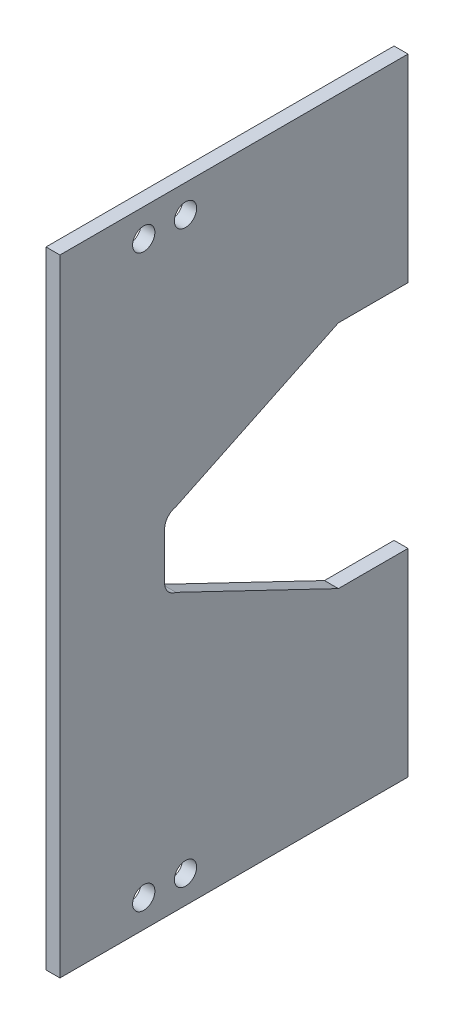
SolidWorks part; units mm, degrees
material "ABS"
ref_plane "前视基准面" through (0, 0, 0) normal (0, 0, 1) x (1, 0, 0)
ref_plane "上视基准面" through (0, 0, 0) normal (0, 1, 0) x (1, 0, 0)
ref_plane "右视基准面" through (0, 0, 0) normal (1, 0, 0) x (0, 0, -1)
ref_plane "基准面4" through (-0.7938, 0, 0) normal (-1, 0, 0) x (0, -1, 0)
sketch "草图1" plane through (-0.7938, 0, 0) normal (-1, 0, 0) x (0, -1, 0)
  line L1 (38.795, 5) -> (12.795, 5)
  line L2 (10.795, 3) -> (10.795, -13)
  line L5 (10.795, 3) -> (55.77, 3) construction
  line L6 (55.77, 3) -> (55.77, -5.0783) construction
  line L7 (55.77, 3) -> (55.77, 5) construction
  line L13 (38.795, 5) -> (72.745, 5)
  line L15 (100.745, 3) -> (100.745, -13)
  line L18 (72.745, 5) -> (98.745, 5)
  line L19 (55.77, 5) -> (55.77, -5.0783) construction
  line L20 (55.77, -5.0783) -> (55.77, -0.0391) construction
  line L21 (55.77, -0.0391) -> (65.77, -0.0391) construction
  line L22 (72.112, -14.1547) -> (62.1308, -0.0391) construction
  line L31 (12.795, -15) -> (47.795, -15)
  line L32 (55.77, -0.0391) -> (50.77, -0.0391)
  line L33 (55.77, -0.0391) -> (60.77, -0.0391)
  line L34 (98.745, -15) -> (63.745, -15)
  line L37 (50.77, -0.0391) -> (47.795, -15)
  line L38 (60.77, -0.0391) -> (63.745, -15)
  arc A2 (12.795, 5) -> (10.795, 3) centre (12.795, 3) ccw
  arc A3 (10.795, -13) -> (12.795, -15) centre (12.795, -13) ccw
  arc A12 (98.745, 5) -> (100.745, 3) centre (98.745, 3) cw
  arc A13 (100.745, -13) -> (98.745, -15) centre (98.745, -13) cw
extrude "凸台-拉伸1" add sketch "草图1" against normal blind 2
fillet "圆角1" radius 2 1 edges at (0.2062, -50.77, -0.0391)
fillet "圆角2" radius 2 1 edges at (0.2063, -47.795, -15)
fillet "圆角3" radius 2 1 edges at (0.2062, -60.77, -0.0391)
fillet "圆角4" radius 2 1 edges at (0.2063, -63.745, -15)
sketch "草图2" plane through (-0.7938, 0, 0) normal (-1, 0, 0) x (0, 0, 1)
  line L0 (5, -55.77) -> (15, -55.77) construction
  line L1 (5, -98.745) -> (5, -12.795) construction
  line L2 (15, -55.77) -> (15, -10.795) construction
  line L3 (15, -55.77) -> (15, -100.745) construction
  line L4 (15, -100.745) -> (3, -100.745) construction
  line L5 (3, -100.745) -> (3, -10.795) construction
  line L6 (3, -10.795) -> (15, -10.795) construction
  line L7 (3, -10.795) -> (15, -10.795)
  line L8 (15, -10.795) -> (15, -100.745)
  line L9 (15, -100.745) -> (3, -100.745)
  line L10 (3, -100.745) -> (3, -10.795)
  line L11 (-15, -29.4743) -> (-25, -29.4743) construction
  line L12 (-15, -12.795) -> (-15, -46.1535) construction
  line L13 (-25, -29.4743) -> (-25, -82.0657) construction
  line L14 (-25, -82.0657) -> (-25, -100.745) construction
  line L15 (-25, -100.745) -> (-13, -100.745) construction
  line L16 (-13, -100.745) -> (-13, -10.795) construction
  line L17 (-13, -10.795) -> (-25, -10.795) construction
  line L18 (-25, -10.795) -> (-25, -29.4743) construction
  line L19 (-1.6491, -50.4499) -> (-13.3901, -48.1151) construction
  line L20 (-13.3901, -48.1151) -> (-25, -45.8065) construction
  line L21 (-1.6491, -61.0901) -> (-13.3901, -63.4249) construction
  line L22 (-13.3901, -63.4249) -> (-25, -65.7335) construction
  line L23 (-25, -10.795) -> (-25, -45.8065)
  line L24 (-25, -45.8065) -> (-13.3901, -48.1151)
  line L26 (-13, -10.795) -> (-25, -10.795)
  line L27 (-13, -10.795) -> (-13.3901, -48.1151)
  line L28 (-13.3901, -63.4249) -> (-25, -65.7335)
  line L29 (-25, -65.7335) -> (-25, -100.745)
  line L30 (-25, -100.745) -> (-13, -100.745)
  line L31 (-13, -100.745) -> (-13.3901, -63.4249)
extrude "凸台-拉伸2" add sketch "草图2" against normal blind 2
sketch "草图5" plane through (1.2062, 0, 0) normal (1, 0, 0) x (0, 0, -1)
  line L0 (25, -10.795) -> (25, -45.8065) construction
  line L1 (25, -45.8065) -> (25, -28.3007) construction
  line L2 (25, -28.3007) -> (25, -37.0536) construction
  line L3 (25, -37.0536) -> (25, -45.8065) construction
  line L4 (25, -45.8065) -> (25, -41.43) construction
  line L5 (25, -41.43) -> (1.6491, -50.4499) construction
  line L6 (1.6491, -50.4499) -> (25, -45.8065)
  line L9 (0.0391, -55.77) -> (-15, -55.77) construction
  line L10 (0.0391, -52.4115) -> (0.0391, -59.1285) construction
  line L11 (-15, -100.745) -> (-15, -10.795) construction
  line L15 (25, -41.43) -> (25, -37.0536) construction
  line L16 (25, -37.0536) -> (25, -39.2418) construction
  line L17 (25, -39.2418) -> (1.6491, -50.4499) construction
  line L18 (1.6491, -50.4499) -> (25, -39.2418)
  line L19 (25, -39.2418) -> (25, -45.8065)
  line L20 (25, -72.2982) -> (25, -65.7335)
  line L21 (1.6491, -61.0901) -> (25, -65.7335)
  line L22 (1.6491, -61.0901) -> (25, -72.2982)
extrude "切除-拉伸1" cut sketch "草图5" against normal blind 10
sketch "草图7" plane through (1.2062, 0, 0) normal (1, 0, 0) x (0, 0, -1)
  line L0 (-15, -55.77) -> (0.0391, -55.77) construction
  line L1 (-15, -100.745) -> (-15, -10.795) construction
  line L2 (0.0391, -52.4115) -> (0.0391, -59.1285) construction
  line L3 (0.0391, -10.795) -> (0.0391, -14.795) construction
  line L4 (-15, -10.795) -> (25, -10.795) construction
  line L5 (-15, -10.795) -> (0.0391, -10.795) construction
  line L6 (0.0391, -14.795) -> (3.0391, -14.795) construction
  line L7 (0.0391, -14.795) -> (-2.9609, -14.795) construction
  circle A0 centre (-2.9609, -14.795) radius 1.6
  circle A1 centre (3.0391, -14.795) radius 1.6
  circle A2 centre (3.0391, -96.745) radius 1.6
  circle A3 centre (-2.9609, -96.745) radius 1.6
extrude "切除-拉伸2" cut sketch "草图7" against normal blind 10
sketch "草图8" plane through (-0.7938, 0, 0) normal (-1, 0, 0) x (0, 0, 1)
  line L0 (-25, -100.745) -> (-35, -100.745) construction
  line L1 (-35, -100.745) -> (-35, -72.2982) construction
  line L2 (-35, -72.2982) -> (-25, -72.2982) construction
  line L3 (-25, -10.795) -> (-35, -10.795) construction
  line L4 (-25, -39.2418) -> (-35, -39.2418) construction
  line L5 (-35, -39.2418) -> (-35, -10.795) construction
  line L6 (-35, -10.795) -> (-25, -10.795)
  line L7 (-25, -10.795) -> (-25, -39.2418)
  line L8 (-35, -10.795) -> (-35, -39.2418)
  line L9 (-35, -39.2418) -> (-25, -39.2418)
  line L10 (-35, -72.2982) -> (-25, -72.2982)
  line L11 (-25, -72.2982) -> (-25, -100.745)
  line L12 (-25, -100.745) -> (-35, -100.745)
  line L13 (-35, -100.745) -> (-35, -72.2982)
extrude "凸台-拉伸3" add sketch "草图8" against normal blind 2
